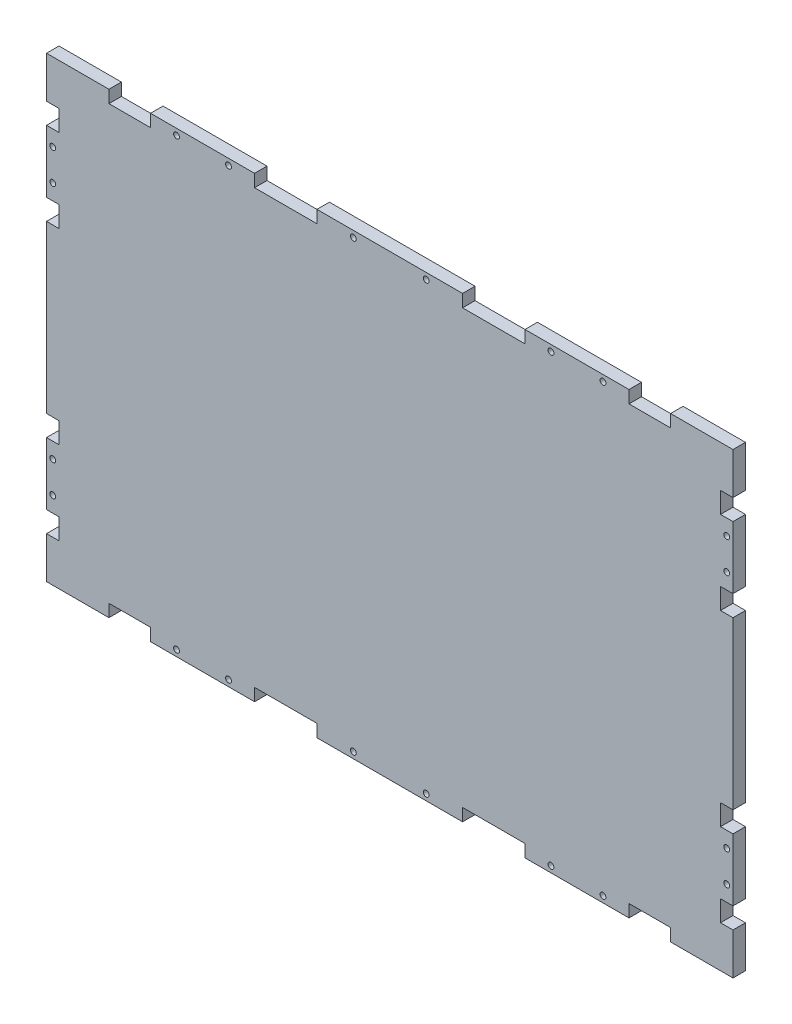
SolidWorks part; units mm, degrees
ref_plane "Plan de face" through (0, 0, 0) normal (0, 0, 1) x (1, 0, 0)
ref_plane "Plan de dessus" through (0, 0, 0) normal (0, 1, 0) x (1, 0, 0)
ref_plane "Plan de droite" through (0, 0, 0) normal (1, 0, 0) x (0, 0, -1)
sketch "Esquisse1" plane through (0, 0, 0) normal (0, 0, 1) x (1, 0, 0)
  line L0 (0, 124.9429) -> (0, -204.46) construction
  line L1 (-165, 110) -> (165, 110)
  line L2 (-165, 110) -> (-165, -110)
  line L3 (-165, -110) -> (165, -110)
  line L4 (165, 110) -> (165, -110)
  line L5 (-211.9802, 0) -> (248.5953, 0) construction
  dimension "D1" = 220
  dimension "D2" = 330
  dimension "D3" = 165
  dimension "D4" = 110
extrude "Boss.-Extru.1" add sketch "Esquisse1" along normal blind 6
sketch "Esquisse3" plane through (0, 0, 6) normal (0, 0, 1) x (1, 0, 0)
  line L0 (0, 140.8551) -> (0, -222.4606) construction
  line L1 (330.3485, 0) -> (-244.4866, 0) construction
  line L2 (165, 110) -> (-165, 110) construction
  line L3 (-135, 110) -> (-115, 110)
  line L4 (-135, 110) -> (-135, 104)
  line L5 (-135, 104) -> (-115, 104)
  line L6 (-115, 110) -> (-115, 104)
  line L7 (-165, 110) -> (-165, -110) construction
  line L8 (-65, 110) -> (-35, 110)
  line L9 (-65, 110) -> (-65, 104)
  line L10 (-65, 104) -> (-35, 104)
  line L11 (-35, 110) -> (-35, 104)
  line L12 (-165, 50) -> (-159, 50)
  line L13 (-165, 50) -> (-165, 40)
  line L14 (-165, 40) -> (-159, 40)
  line L15 (-159, 50) -> (-159, 40)
  line L16 (35, 110) -> (35, 104)
  line L17 (-165, 90) -> (-159, 90)
  line L18 (-165, 90) -> (-165, 80)
  line L19 (-165, 80) -> (-159, 80)
  line L20 (-159, 90) -> (-159, 80)
  line L21 (65, 104) -> (35, 104)
  line L22 (65, 110) -> (35, 110)
  line L23 (159, 90) -> (159, 80)
  line L24 (165, 80) -> (159, 80)
  line L25 (165, 90) -> (165, 80)
  line L26 (165, 90) -> (159, 90)
  line L27 (159, 50) -> (159, 40)
  line L28 (165, 40) -> (159, 40)
  line L29 (165, 50) -> (165, 40)
  line L30 (165, 50) -> (159, 50)
  line L31 (65, 110) -> (65, 104)
  line L32 (115, 110) -> (115, 104)
  line L33 (135, 104) -> (115, 104)
  line L34 (135, 110) -> (135, 104)
  line L35 (135, 110) -> (115, 110)
  line L36 (135, -110) -> (115, -110)
  line L37 (135, -110) -> (135, -104)
  line L38 (135, -104) -> (115, -104)
  line L39 (115, -110) -> (115, -104)
  line L40 (65, -110) -> (65, -104)
  line L41 (165, -50) -> (159, -50)
  line L42 (165, -50) -> (165, -40)
  line L43 (165, -40) -> (159, -40)
  line L44 (159, -50) -> (159, -40)
  line L45 (165, -90) -> (159, -90)
  line L46 (165, -90) -> (165, -80)
  line L47 (165, -80) -> (159, -80)
  line L48 (159, -90) -> (159, -80)
  line L49 (65, -110) -> (35, -110)
  line L50 (65, -104) -> (35, -104)
  line L51 (-159, -90) -> (-159, -80)
  line L52 (-165, -80) -> (-159, -80)
  line L53 (-165, -90) -> (-165, -80)
  line L54 (-165, -90) -> (-159, -90)
  line L55 (35, -110) -> (35, -104)
  line L56 (-159, -50) -> (-159, -40)
  line L57 (-165, -40) -> (-159, -40)
  line L58 (-165, -50) -> (-165, -40)
  line L59 (-165, -50) -> (-159, -50)
  line L60 (-35, -110) -> (-35, -104)
  line L61 (-65, -104) -> (-35, -104)
  line L62 (-65, -110) -> (-65, -104)
  line L63 (-65, -110) -> (-35, -110)
  line L64 (-115, -110) -> (-115, -104)
  line L65 (-135, -104) -> (-115, -104)
  line L66 (-135, -110) -> (-135, -104)
  line L67 (-135, -110) -> (-115, -110)
  dimension "D1" = 20
  dimension "D2" = 30
  dimension "D3" = 6
  dimension "D4" = 6
  dimension "D5" = 6
  dimension "D6" = 10
  dimension "D7" = 6
  dimension "D8" = 10
  dimension "D9" = 30
  dimension "D10" = 50
  dimension "D11" = 20
  dimension "D12" = 30
extrude "Enlèv. mat.-Extru.2" cut sketch "Esquisse3" against normal blind 6
sketch "Esquisse4" plane through (0, 0, 6) normal (0, 0, 1) x (1, 0, 0)
  line L0 (0, 191.3584) -> (0, -190.3505) construction
  line L1 (361.8037, 0) -> (-270.0648, 0) construction
  line L2 (-165, 80) -> (-165, 50) construction
  line L3 (-115, 104) -> (-115, 110) construction
  line L4 (-65, 110) -> (-115, 110) construction
  line L5 (35, 110) -> (-35, 110) construction
  line L6 (-35, 104) -> (-35, 110) construction
  line L7 (-65, 110) -> (-65, 104) construction
  line L8 (-165, 80) -> (-159, 80) construction
  line L9 (-159, 50) -> (-165, 50) construction
  circle A0 centre (-102.5, 107) radius 1.4
  circle A1 centre (-77.5, 107) radius 1.4
  circle A2 centre (-17.5, 107) radius 1.4
  circle A3 centre (-162, 72.5) radius 1.4
  circle A4 centre (-162, 57.5) radius 1.4
  circle A5 centre (162, 57.5) radius 1.4
  circle A6 centre (162, 72.5) radius 1.4
  circle A7 centre (17.5, 107) radius 1.4
  circle A8 centre (77.5, 107) radius 1.4
  circle A9 centre (102.5, 107) radius 1.4
  circle A10 centre (102.5, -107) radius 1.4
  circle A11 centre (77.5, -107) radius 1.4
  circle A12 centre (17.5, -107) radius 1.4
  circle A13 centre (162, -72.5) radius 1.4
  circle A14 centre (162, -57.5) radius 1.4
  circle A15 centre (-162, -57.5) radius 1.4
  circle A16 centre (-162, -72.5) radius 1.4
  circle A17 centre (-17.5, -107) radius 1.4
  circle A18 centre (-77.5, -107) radius 1.4
  circle A19 centre (-102.5, -107) radius 1.4
  point P29 (-162, 50)
  dimension "D1" = 2.8
  dimension "D2" = 2.8
  dimension "D3" = 2.8
  dimension "D4" = 2.8
  dimension "D5" = 2.8
  dimension "D6" = 3
  dimension "D7" = 3
  dimension "D8" = 12.5
  dimension "D9" = 3
  dimension "D10" = 3
  dimension "D11" = 3
  dimension "D12" = 17.5
  dimension "D13" = 12.5
  dimension "D14" = 7.5
  dimension "D15" = 7.5
extrude "Enlèv. mat.-Extru.3" cut sketch "Esquisse4" against normal blind 6
equation "\"D3@Esquisse1\"=\"D2@Esquisse1\"/2"
equation "\"D4@Esquisse1\"=\"D1@Esquisse1\"/2"
